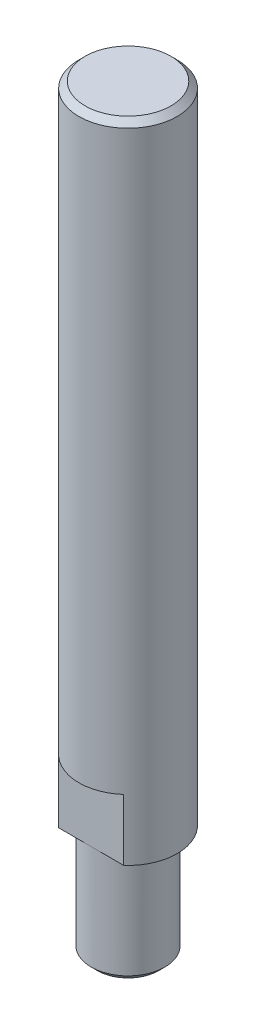
SolidWorks part; units mm, degrees
material "AISI 1045 Aço, trefilado"
ref_plane "Plano frontal" through (0, 0, 0) normal (0, 0, 1) x (1, 0, 0)
ref_plane "Plano superior" through (0, 0, 0) normal (0, 1, 0) x (1, 0, 0)
ref_plane "Plano direito" through (0, 0, 0) normal (1, 0, 0) x (0, 0, -1)
sketch "Esboço1" plane through (0, 0, 0) normal (0, 1, 0) x (1, 0, 0)
  circle A0 centre (0, 0) radius 8
  dimension "D1" = 16
extrude "Ressalto-extrusão1" add sketch "Esboço1" along normal blind 105
cosmetic thread "Representação de rosca1" parameters "D1"=40, "D2"=13.797
sketch "Esboço2" plane through (0, 0, 0) normal (0, -1, 0) x (1, 0, 0)
  circle A0 centre (0, 0) radius 6
  dimension "D1" = 12
extrude "Ressalto-extrusão2" add sketch "Esboço2" along normal blind 18
cosmetic thread "Representação de rosca2" parameters "D2"=10.072
chamfer "Chanfro1" distance 1 angle 45 2 edges at (0, -18, -6) (0, 105, 8)
sketch "Esboço3" plane through (0, 0, 0) normal (0, -1, 0) x (1, 0, 0)
  line L0 (-8, 0) -> (8, 0) construction
  line L1 (-8, 6) -> (8, 6)
  line L2 (-8, -6) -> (8, -6)
  circle A0 centre (0, 0) radius 8 construction
  arc A1 (-8, 6) -> (-8, -6) centre (-8, 0) ccw
  arc A2 (8, -6) -> (8, 6) centre (8, 0) ccw
  point P5 (0, 0)
  dimension "D1" = 6
extrude "Corte-extrusão1" cut sketch "Esboço3" against normal blind 10 flip side to cut
